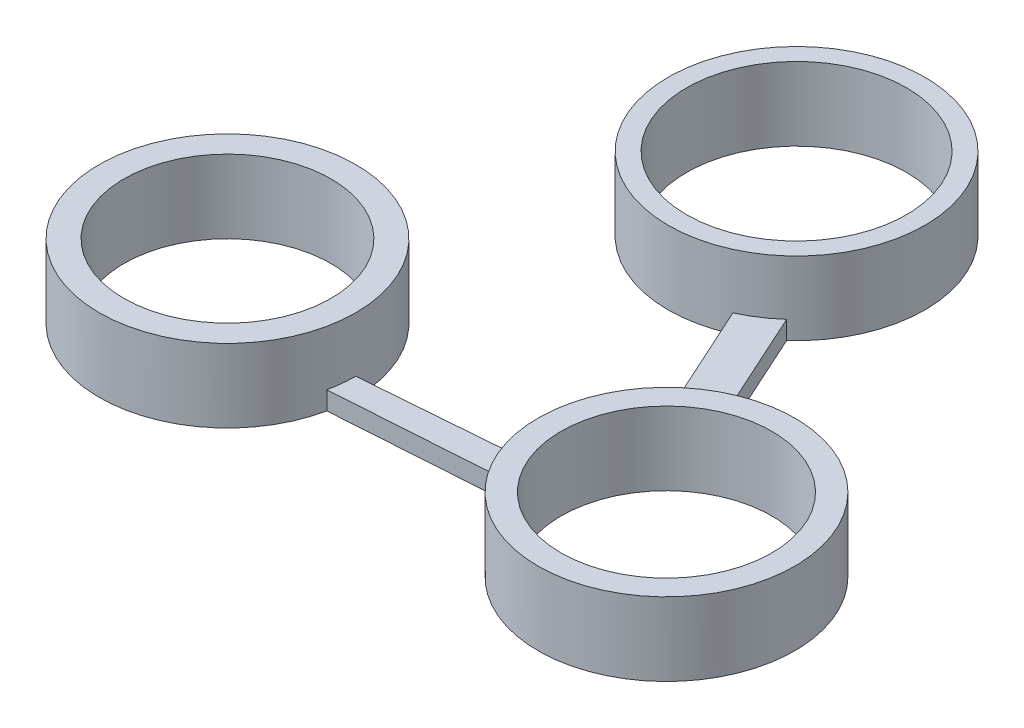
SolidWorks part; units mm, degrees
ref_plane "前视基准面" through (0, 0, 0) normal (0, 0, 1) x (1, 0, 0)
ref_plane "上视基准面" through (0, 0, 0) normal (0, 1, 0) x (1, 0, 0)
ref_plane "右视基准面" through (0, 0, 0) normal (1, 0, 0) x (0, 0, -1)
sketch "草图1" plane through (0, 0, 0) normal (0, 1, 0) x (1, 0, 0)
  circle A0 centre (-73.7352, 44.2897) radius 5.65
  circle A1 centre (-73.7352, 44.2897) radius 7
  circle A2 centre (-49.7881, 44.2897) radius 5.75
  circle A3 centre (-49.7881, 44.2897) radius 7
  circle A4 centre (-62.341, 63.9393) radius 6
  circle A5 centre (-62.341, 63.9393) radius 7
  dimension "D1" = 14
  dimension "D2" = 11.3
  dimension "D3" = 14
  dimension "D4" = 11.5
  dimension "D5" = 14
  dimension "D6" = 12
extrude "凸台-拉伸1" add sketch "草图1" along normal blind 4
sketch "草图2" plane through (0, 0, 0) normal (0, 1, 0) x (1, 0, 0)
  line L0 (-66.7352, 44.2897) -> (-56.7438, 45.0759)
  line L1 (-66.7352, 44.2897) -> (-67.1135, 42.842)
  line L2 (-67.1135, 42.842) -> (-56.372, 43.5659)
  line L3 (-56.372, 43.5659) -> (-56.7438, 45.0759)
  line L4 (-59.4428, 57.5675) -> (-55.3416, 48.551)
  line L5 (-55.3416, 48.551) -> (-53.588, 49.7512)
  line L6 (-53.588, 49.7512) -> (-57.6701, 58.7256)
  line L7 (-57.6701, 58.7256) -> (-59.4428, 57.5675)
  circle A1 centre (-73.7352, 44.2897) radius 7 construction
  circle A2 centre (-49.7881, 44.2897) radius 7 construction
  circle A3 centre (-62.341, 63.9393) radius 7 construction
  circle A4 centre (-49.7881, 44.2897) radius 7 construction
extrude "凸台-拉伸2" add sketch "草图2" along normal blind 1
